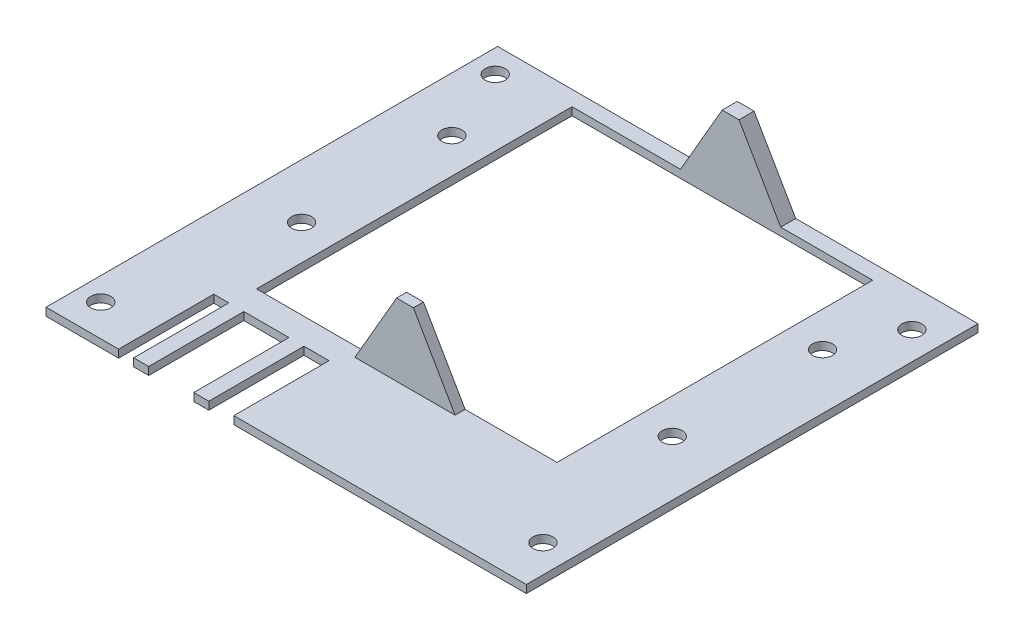
SolidWorks part; units mm, degrees
other "DetailItem1"
material "ABS"
ref_plane "Front Plane" through (0, 0, 0) normal (0, 0, 1) x (1, 0, 0)
ref_plane "Top Plane" through (0, 0, 0) normal (0, 1, 0) x (1, 0, 0)
ref_plane "Right Plane" through (0, 0, 0) normal (1, 0, 0) x (0, 0, -1)
sketch "Sketch1" plane through (0, 0, 0) normal (0, 1, 0) x (1, 0, 0)
  line L1 (-32.2441, 108.719) -> (64.6459, 108.719)
  line L2 (-32.2441, 108.719) -> (-32.2441, 18.549)
  line L3 (-32.2441, 18.549) -> (64.6459, 18.549)
  line L4 (64.6459, 108.719) -> (64.6459, 18.549)
  dimension "D1" = 96.89
  dimension "D2" = 90.17
extrude "PCB" add sketch "Sketch1" along normal blind 1.57
sketch "Sketch2" plane through (0, 1.57, 0) normal (0, 1, 0) x (1, 0, 0)
  line L1 (-32.2441, 18.549) -> (64.6459, 18.549) construction
  line L2 (-32.2441, 108.719) -> (-32.2441, 18.549) construction
  line L3 (-32.2441, 18.549) -> (64.6459, 18.549) construction
  circle A0 centre (58.5659, 27.439) radius 2
  circle A1 centre (-27.1641, 24.899) radius 2
  circle A2 centre (-27.1641, 103.639) radius 2
  circle A3 centre (58.5659, 101.099) radius 2
  dimension "D3" = 4
  dimension "D6" = 4
  dimension "D11" = 4
  dimension "D12" = 4
  dimension "D2" = 90.81
  dimension "D4" = 90.81
  dimension "D5" = 6.35
  dimension "D7" = 5.08
  dimension "D8" = 5.08
  dimension "D9" = 82.55
  dimension "D10" = 85.09
  dimension "D13" = 8.89
extrude "M3 Mounting Holes" cut sketch "Sketch2" against normal blind 1.57
sketch "Sketch3" plane through (0, 1.57, 0) normal (0, 1, 0) x (1, 0, 0)
  line L0 (64.6459, 108.719) -> (-32.2441, 108.719) construction
  line L1 (12.7559, 108.719) -> (22.7559, 108.719)
  line L2 (12.7559, 108.719) -> (12.7559, 105.719)
  line L3 (12.7559, 105.719) -> (22.7559, 105.719)
  line L4 (22.7559, 108.719) -> (22.7559, 105.719)
  line L5 (-32.2441, 108.719) -> (-32.2441, 18.549) construction
  line L7 (12.7559, 42.719) -> (22.7559, 42.719)
  line L8 (12.7559, 42.719) -> (12.7559, 40.719)
  line L9 (12.7559, 40.719) -> (22.7559, 40.719)
  line L10 (22.7559, 42.719) -> (22.7559, 40.719)
  dimension "D1" = 3
  dimension "D2" = 10
  dimension "D3" = 0
  dimension "D4" = 45
  dimension "D5" = 63
  dimension "D6" = 2
  dimension "D7" = 45
extrude "Boss-Extrude1" [suppressed] add sketch "Sketch3" along normal blind 10
sketch "Sketch4" plane through (0, 1.57, 0) normal (0, 1, 0) x (1, 0, 0)
  line L0 (64.6459, 108.719) -> (-32.2441, 108.719) construction
  line L1 (64.6459, 108.719) -> (-32.2441, 108.719) construction
  line L2 (-32.2441, 108.719) -> (-32.2441, 18.549) construction
  line L3 (64.6459, 108.719) -> (-32.2441, 108.719) construction
  circle A0 centre (-20.8941, 88.719) radius 2
  circle A1 centre (53.1059, 88.719) radius 2
  circle A2 centre (-20.8941, 58.719) radius 2
  circle A3 centre (53.1059, 58.719) radius 2
  dimension "D1" = 4
  dimension "D2" = 4
  dimension "D7" = 4
  dimension "D8" = 4
  dimension "D12" = 74
  dimension "D3" = 20
  dimension "D4" = 20
  dimension "D5" = 74
  dimension "D6" = 11.35
  dimension "D9" = 50
  dimension "D10" = 50
  dimension "D11" = 11.35
extrude "Cut-Extrude1" cut sketch "Sketch4" against normal blind 23
ref_plane "Plane1" through (0, 0, -42.719) normal (0, 0, 1) x (1, 0, 0)
sketch "Sketch7" plane through (0, 0, -42.719) normal (0, 0, 1) x (1, 0, 0)
  line L0 (27.7559, 1.57) -> (19.4384, 15.9764)
  line L1 (19.4384, 15.9764) -> (16.0735, 15.9764)
  line L2 (16.0735, 15.9764) -> (7.7559, 1.57)
  line L3 (7.7559, 1.57) -> (27.7559, 1.57)
  line L4 (-32.2441, 1.57) -> (64.6459, 1.57) construction
  dimension "D1" = 60
  dimension "D2" = 60
  dimension "D3" = 0
  dimension "D4" = 3.3649
  dimension "D5" = 20
  dimension "D6" = 5
ref_plane "Plane2" through (0, 0, -108.719) normal (0, 0, 1) x (1, 0, 0)
sketch "Sketch8" plane through (0, 0, -108.719) normal (0, 0, 1) x (1, 0, 0)
  line L0 (27.7559, 1.57) -> (19.4384, 15.9764) construction
  line L1 (19.4384, 15.9764) -> (16.0735, 15.9764) construction
  line L2 (16.0735, 15.9764) -> (7.7559, 1.57) construction
  line L3 (7.7559, 1.57) -> (27.7559, 1.57) construction
  line L4 (27.7559, 1.57) -> (19.4384, 15.9764)
  line L5 (19.4384, 15.9764) -> (16.0735, 15.9764)
  line L6 (16.0735, 15.9764) -> (7.7559, 1.57)
  line L7 (7.7559, 1.57) -> (27.7559, 1.57)
extrude "Boss-Extrude2" add sketch "Sketch7" along normal blind 2
extrude "Boss-Extrude3" add sketch "Sketch8" along normal blind 3
sketch "Sketch9" plane through (0, 1.57, 0) normal (0, 1, 0) x (1, 0, 0)
  line L0 (-32.2441, 18.549) -> (64.6459, 18.549) construction
  line L1 (-14.2441, 18.549) -> (-17.2441, 18.549)
  line L2 (-14.2441, 18.549) -> (-14.2441, 37.549)
  line L3 (-14.2441, 37.549) -> (-17.2441, 37.549)
  line L4 (-17.2441, 18.549) -> (-17.2441, 37.549)
  line L5 (-32.2441, 108.719) -> (-32.2441, 18.549) construction
  line L6 (-11.2441, 18.549) -> (-2.2441, 18.549)
  line L7 (-11.2441, 18.549) -> (-11.2441, 37.549)
  line L8 (-11.2441, 37.549) -> (-2.2441, 37.549)
  line L9 (-2.2441, 18.549) -> (-2.2441, 37.549)
  line L11 (0.7559, 18.549) -> (5.7559, 18.549)
  line L12 (0.7559, 18.549) -> (0.7559, 37.549)
  line L13 (0.7559, 37.549) -> (5.7559, 37.549)
  line L14 (5.7559, 18.549) -> (5.7559, 37.549)
  dimension "D1" = 19
  dimension "D2" = 19
  dimension "D3" = 3
  dimension "D4" = 3
  dimension "D5" = 9
  dimension "D6" = 15
  dimension "D7" = 5
  dimension "D8" = 19
  dimension "D9" = 3
extrude "Cut-Extrude2" cut sketch "Sketch9" against normal through all
sketch "Sketch10" plane through (0, 1.57, 0) normal (0, 1, 0) x (1, 0, 0)
  line L0 (7.7559, 108.719) -> (-32.2441, 108.719) construction
  line L1 (-32.2441, 18.549) -> (-31.7441, 18.549)
  line L2 (-32.2441, 18.549) -> (-32.2441, 108.719)
  line L3 (-32.2441, 108.719) -> (-31.7441, 108.719)
  line L4 (-31.7441, 18.549) -> (-31.7441, 108.719)
  line L5 (64.6459, 108.719) -> (27.7559, 108.719) construction
  line L6 (64.6459, 18.549) -> (64.1459, 18.549)
  line L7 (64.6459, 18.549) -> (64.6459, 108.719)
  line L8 (64.6459, 108.719) -> (64.1459, 108.719)
  line L9 (64.1459, 18.549) -> (64.1459, 108.719)
  dimension "D1" = 0.5
  dimension "D2" = 0.5
extrude "Cut-Extrude3" cut sketch "Sketch10" against normal blind 10
sketch "Sketch11" plane through (0, 1.57, 0) normal (0, 1, 0) x (1, 0, 0)
  line L0 (7.7559, 105.719) -> (27.7559, 105.719) construction
  line L1 (-13.8941, 105.719) -> (46.1059, 105.719)
  line L2 (-13.8941, 105.719) -> (-13.8941, 42.719)
  line L3 (-13.8941, 42.719) -> (46.1059, 42.719)
  line L4 (46.1059, 105.719) -> (46.1059, 42.719)
  dimension "D1" = 60
  dimension "D2" = 63
  dimension "D3" = 0
  dimension "D4" = 7
extrude "Cut-Extrude4" cut sketch "Sketch11" against normal blind 10
